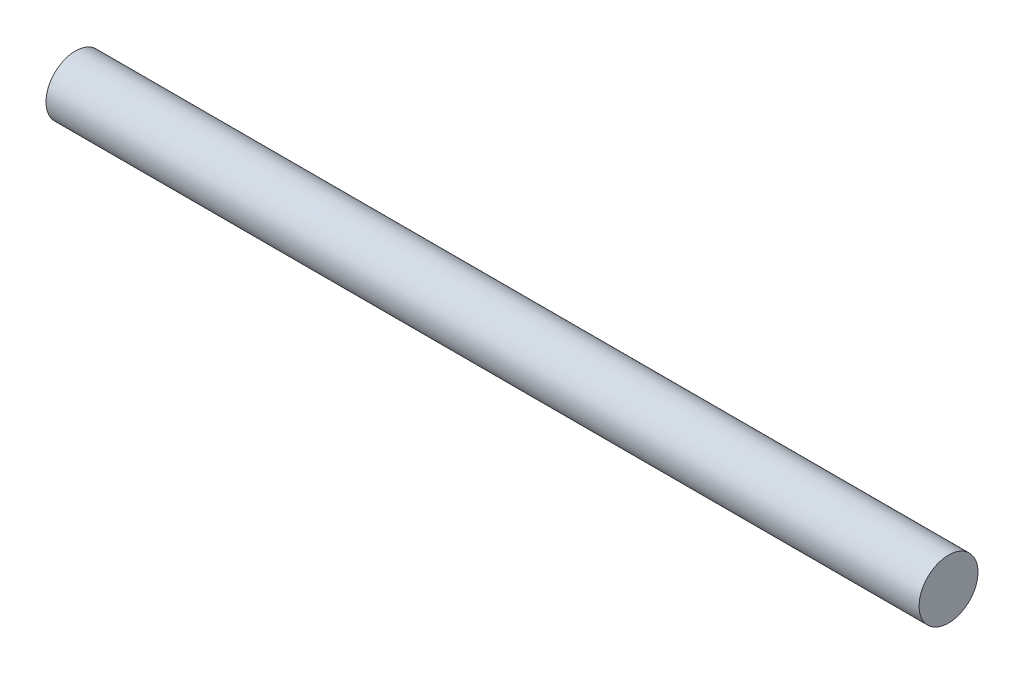
SolidWorks part; units mm, degrees
material "6061-T6 (SS)"
ref_plane "Front Plane" through (0, 0, 0) normal (0, 0, 1) x (1, 0, 0)
ref_plane "Top Plane" through (0, 0, 0) normal (0, 1, 0) x (1, 0, 0)
ref_plane "Right Plane" through (0, 0, 0) normal (1, 0, 0) x (0, 0, -1)
sketch "Sketch1" plane through (0, 0, 0) normal (1, 0, 0) x (0, 0, -1)
  circle A0 centre (0, 0) radius 6
  dimension "D1" = 12
extrude "Boss-Extrude1" add sketch "Sketch1" along normal blind 177.8
